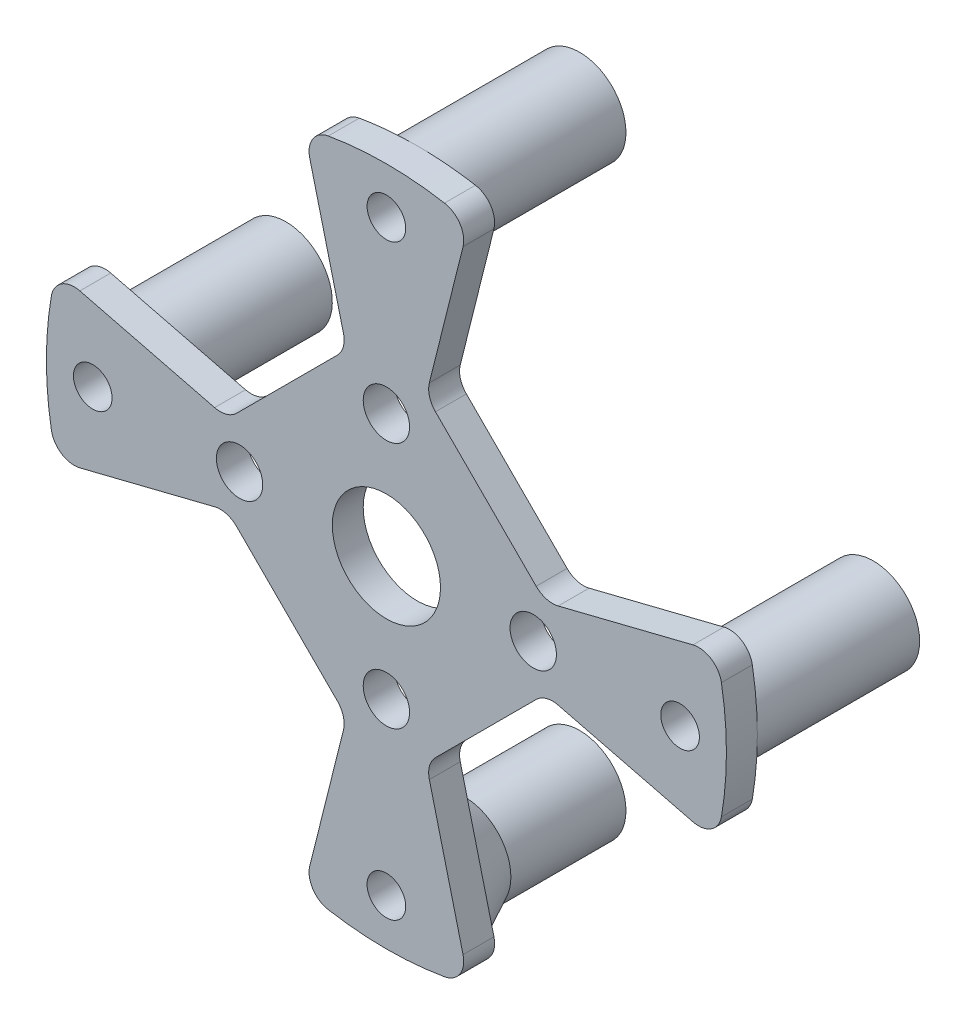
SolidWorks part; units mm, degrees
ref_plane "前视基准面" through (0, 0, 0) normal (0, 0, 1) x (1, 0, 0)
ref_plane "上视基准面" through (0, 0, 0) normal (0, 1, 0) x (1, 0, 0)
ref_plane "右视基准面" through (0, 0, 0) normal (1, 0, 0) x (0, 0, -1)
sketch "草图1" plane through (0, 0, 0) normal (0, 0, 1) x (1, 0, 0)
  circle A0 centre (0, 0) radius 22
extrude "凸台-拉伸1" add sketch "草图1" along normal blind 2
sketch "草图3" plane through (0, 0, 0) normal (0, 0, -1) x (-1, 0, 0)
  circle A4 centre (0, 0) radius 8 construction
  circle A5 centre (0, 0) radius 9.5 construction
  circle A6 centre (9.5, 0) radius 1.5
  circle A7 centre (0, 8) radius 1.5
extrude "切除-拉伸1" cut sketch "草图3" against normal blind 3
sketch "草图4" plane through (0, 0, 0) normal (0, 0, -1) x (-1, 0, 0)
  circle A0 centre (0, 0) radius 3.5
extrude "切除-拉伸2" cut sketch "草图4" against normal blind 3
sketch "草图6" plane through (0, 0, 0) normal (0, 0, -1) x (-1, 0, 0)
  line L0 (0, -7.5) -> (0, -22) construction
  circle A1 centre (0, 0) radius 22 construction
  circle A2 centre (0, -19) radius 3
extrude "凸台-拉伸3" add sketch "草图6" along normal blind 10.5
sketch "草图8" plane through (0, 0, -10.5) normal (0, 0, -1) x (-1, 0, 0)
  circle A0 centre (0, -19) radius 1.25
extrude "切除-拉伸4" cut sketch "草图8" along a picked direction on the side against the normal blind 12.5
sketch "草图7" plane through (0, 0, 0) normal (0, 0, -1) x (-1, 0, 0)
  line L0 (-6, 0) -> (0, 6) construction
  line L1 (0, 0) -> (-6, 1.5) construction
  line L2 (-6, 1.5) -> (-25.0731, 6.2683) construction
  line L3 (0, 0) -> (-1.5, 6) construction
  line L4 (-1.5, 6) -> (-6.7018, 26.8073) construction
  line L5 (-2.5727, 10.291) -> (-10.291, 2.5727)
  line L6 (-7.6282, 30.5128) -> (-30.5128, 7.6282)
  line L7 (-10.291, 2.5727) -> (-30.5128, 7.6282)
  line L8 (-7.6282, 30.5128) -> (-2.5727, 10.291)
extrude "切除-拉伸3" cut sketch "草图7" against normal blind 6
pattern_circular "阵列(圆周)1" count 4 over 360 about axis through (0, 0, 0) along (0, 0, 1) of "凸台-拉伸3", "切除-拉伸4", "切除-拉伸3"
fillet "圆角2" radius 1.5 8 edges at (-21.3431, 5.3358, 1) (-21.3431, -5.3358, 1) (-5.3358, -21.3431, 1) (5.3358, -21.3431, 1) (21.3431, -5.3358, 1) (21.3431, 5.3358, 1) (5.3358, 21.3431, 1) (-5.3358, 21.3431, 1)
fillet "圆角3" radius 1.5 8 edges at (-2.5727, -10.291, 1) (-10.291, -2.5727, 1) (2.5727, -10.291, 1) (10.291, -2.5727, 1) (10.291, 2.5727, 1) (2.5727, 10.291, 1) (-2.5727, 10.291, 1) (-10.291, 2.5727, 1)
pattern_circular "阵列(圆周)2" count 2 every 180 about axis through (0, 0, 0) along (0, 0, 1) of "切除-拉伸1"
ref_axis "基准轴1" through (0, -19, 2) along (0, 0, -1)
sketch "草图10" plane through (0, 0, 0) normal (1, 0, 0) x (0, 0, -1)
  line L0 (10.5, -22) -> (10.5, -16) construction
  line L1 (10.5, -22) -> (10.5, -16) construction
  line L2 (0, -22) -> (0, -16) construction
  line L3 (0, -22) -> (0, -16.3127) construction
  line L4 (0, -16.3127) -> (0, -14.5)
  line L5 (0, -14.5) -> (3.6906, -16.3127)
  line L7 (3.6906, -16.3127) -> (0, -16.3127)
  point P3 (0, -16)
  point P4 (0, 0)
revolve "旋转1" add sketch "草图10" angle 125 about axis through (0, -19, 2) along (0, 0, -1) other way angle 125
